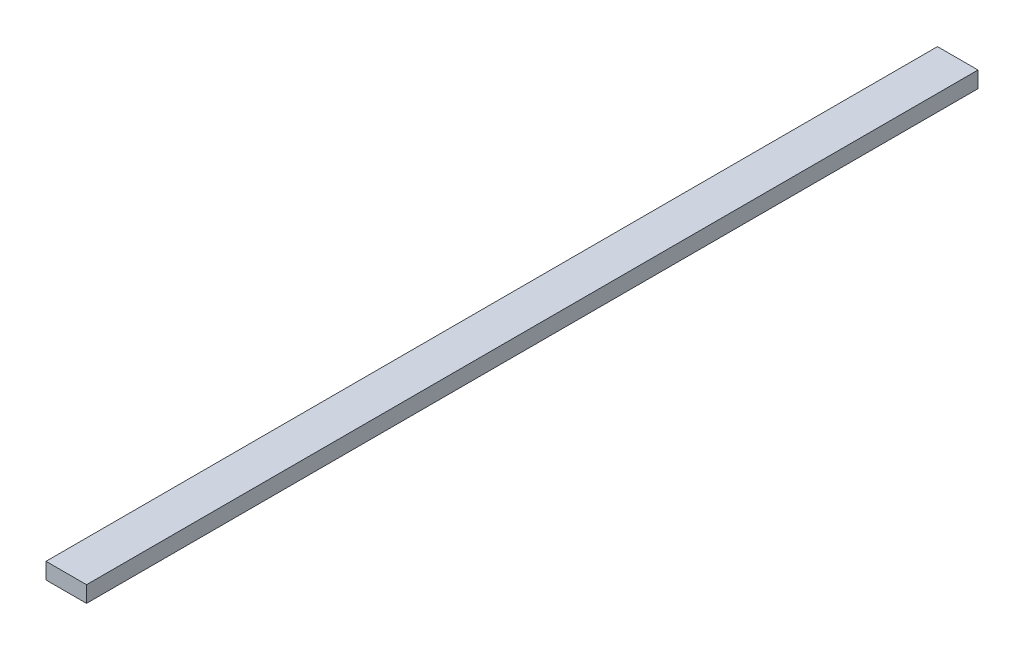
SolidWorks part; units mm, degrees
material "Gray Cast Iron"
ref_plane "Front Plane" through (0, 0, 0) normal (0, 0, 1) x (1, 0, 0)
ref_plane "Top Plane" through (0, 0, 0) normal (0, 1, 0) x (1, 0, 0)
ref_plane "Right Plane" through (0, 0, 0) normal (1, 0, 0) x (0, 0, -1)
sketch "Sketch1" plane through (0, 0, 0) normal (0, 1, 0) x (1, 0, 0)
  line L1 (0, 0) -> (25, 0)
  line L2 (0, 0) -> (0, 550)
  line L3 (0, 550) -> (25, 550)
  line L4 (25, 0) -> (25, 550)
  dimension "D1" = 25
  dimension "D2" = 550
extrude "Boss-Extrude1" add sketch "Sketch1" along normal blind 10
